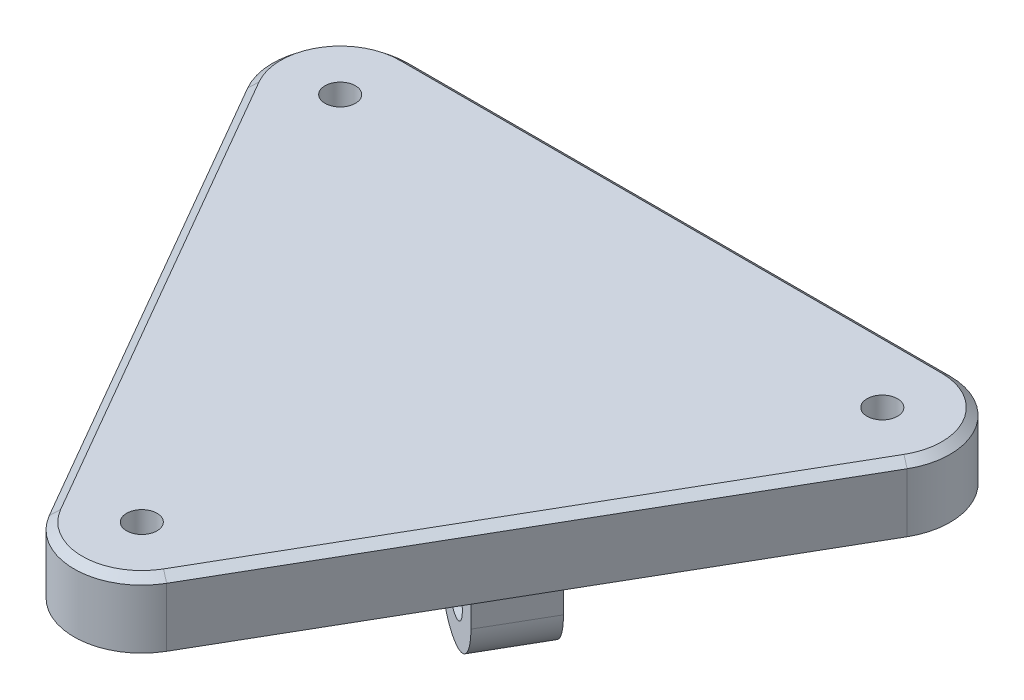
SolidWorks part; units mm, degrees
ref_plane "Front Plane" through (0, 0, 0) normal (0, 0, 1) x (1, 0, 0)
ref_plane "Top Plane" through (0, 0, 0) normal (0, 1, 0) x (1, 0, 0)
ref_plane "Right Plane" through (0, 0, 0) normal (1, 0, 0) x (0, 0, -1)
sketch "Sketch1" plane through (0, 0, 0) normal (0, 1, 0) x (1, 0, 0)
  line L0 (0, 18.75) -> (0, -14.7407) construction
  line L1 (-6.25, 0) -> (6.25, 0) construction
  line L7 (0, 0) -> (-16.238, -9.375) construction
  line L8 (0, 0) -> (16.238, -9.375) construction
  circle A3 centre (0, 0) radius 6.25
  point P2 (5.4127, -3.125)
  point P5 (0, 6.25)
  point P6 (-6.25, 0)
  point P7 (0, -6.25)
  point P8 (6.25, 0)
  point P11 (-5.4127, -3.125)
  dimension "D2" = 12.5
  dimension "D1" = 12.5
  dimension "D3" = 12.5
  dimension "D4" = 12.5
  dimension "D5" = 120
  dimension "D6" = 120
ref_plane "Plane4" through (0, 0, 0) normal (0, 1, 0) x (1, 0, 0)
sketch "Sketch6" plane through (0, 0, 0) normal (0, 1, 0) x (1, 0, 0)
  line L0 (-40, 33.094) -> (40, 33.094)
  line L1 (-28.6603, -16.547) -> (0, 0) construction
  line L2 (0, 0) -> (28.6603, -16.547) construction
  line L3 (28.6603, -16.547) -> (48.6603, 18.094)
  line L4 (-28.6603, -16.547) -> (-48.6603, 18.094)
  line L5 (-28.6603, -16.547) -> (-8.6603, -51.188)
  line L6 (8.6603, -51.188) -> (28.6603, -16.547)
  line L7 (0, 0) -> (-40, 23.094) construction
  line L8 (-40, 23.094) -> (40, 23.094) construction
  line L9 (40, 23.094) -> (0, 0) construction
  line L10 (0, 0) -> (0, -46.188) construction
  line L11 (0, 0) -> (-34.5631, 0) construction
  arc A0 (48.6603, 18.094) -> (40, 33.094) centre (40, 23.094) ccw
  arc A1 (-8.6603, -51.188) -> (8.6603, -51.188) centre (0, -46.188) ccw
  arc A2 (-48.6603, 18.094) -> (-40, 33.094) centre (-40, 23.094) cw
  dimension "D1" = 10
  dimension "D3" = 80
  dimension "D2" = 40
  dimension "D4" = 46.188
extrude "Boss-Extrude3" add sketch "Sketch6" along normal blind 10
ref_plane "Plane5" through (0, 10, 0) normal (0, 1, 0) x (1, 0, 0)
ref_plane "Plane10" through (0, 0, 0) normal (0, -1, 0) x (-1, 0, 0)
sketch "Sketch13" plane through (0, 0, 0) normal (0, -1, 0) x (-1, 0, 0)
  line L2 (-40, 33.094) -> (40, 33.094) construction
  line L3 (-5.25, 26.094) -> (4.75, 26.094)
  line L22 (-5.25, 26.094) -> (-5.25, 14.094)
  line L23 (-5.25, 14.094) -> (4.75, 14.094)
  line L24 (4.75, 14.094) -> (4.75, 26.094)
  point P0 (-0.25, 33.094)
  point P1 (-0.25, 26.094)
  point P5 (0, 33.094)
  dimension "D1" = 7
  dimension "D2" = 0.25
  dimension "D4" = 10
  dimension "D6" = 12
extrude "Boss-Extrude5" add sketch "Sketch13" along normal blind 20
ref_plane "Plane12" through (5.25, 0, 0) normal (1, 0, 0) x (0, 0, -1)
sketch "Sketch15" plane through (5.25, 0, 0) normal (1, 0, 0) x (0, 0, -1)
  line L0 (20.094, 0) -> (20.094, -8) construction
  line L1 (26.094, 0) -> (14.094, 0) construction
  line L2 (14.094, -8) -> (14.094, -20)
  line L3 (14.094, -20) -> (26.094, -20)
  line L4 (26.094, -20) -> (26.094, -8)
  circle A0 centre (20.094, -8) radius 2.55
  arc A1 (14.094, -8) -> (26.094, -8) centre (20.094, -8) ccw
  dimension "D2" = 5.1
  dimension "D1" = 8
extrude "Cut-Extrude7" cut sketch "Sketch15" against normal through all
ref_plane "Plane14" through (0, 10, 0) normal (0, 1, 0) x (1, 0, 0)
sketch "Sketch17" plane through (0, 10, 0) normal (0, 1, 0) x (1, 0, 0)
  line L0 (-40, 33.094) -> (40, 33.094) construction
  line L1 (0, 33.094) -> (0, 23.094) construction
ref_plane "Plane15" through (0, 0, 0) normal (0, -1, 0) x (-1, 0, 0)
ref_plane "Plane16" through (0, 0, 0) normal (0, -1, 0) x (-1, 0, 0)
sketch "Sketch18" plane through (0, 0, 0) normal (0, -1, 0) x (-1, 0, 0)
  point P10 (-40, 23.094)
  point P11 (40, 23.094)
  point P12 (0, -46.188)
ref_plane "Plane17" through (0, 0, 0) normal (0, -1, 0) x (-1, 0, 0)
hole_wizard "CBORE for M4 SHCS1" positions "Sketch19" profile "Sketch20" counterbore size "M4" standard "ANSI Metric"
sketch "Sketch19" plane through (0, 0, 0) normal (0, -1, 0) x (-1, 0, 0)
  point P0 (-40, 23.094)
  point P3 (40, 23.094)
  point P6 (0, -46.188)
sketch "Sketch20" plane through (40, 0, -23.094) normal (1, 0, 0) x (0, 0, -1)
  line L0 (0, 0) -> (0, 16.8519)
  line L1 (0, 16.8519) -> (2.25, 15.5)
  line L2 (2.25, 15.5) -> (2.25, 4)
  line L3 (2.25, 4) -> (4, 4)
  line L4 (4, 4) -> (4, 0)
  line L5 (4, 0) -> (0, 0)
  line L10 (0, 16.8519) -> (-2.25, 15.5) construction
  line L11 (0, -6.35) -> (0, 107.95) construction
  dimension "Hole Dia." = 4.5
  dimension "Hole Depth" = 15.5
  dimension "C'Bore Dia." = 8
  dimension "C'Bore Depth" = 4
  dimension "Drill Angle" = 118
sketch "Sketch21" plane through (0, 0, 0) normal (0, -1, 0) x (-1, 0, 0)
  circle A0 centre (0, 0) radius 1.118
extrude "Boss-Extrude6" add sketch "Sketch21" along normal blind 1
pattern_circular "CirPattern3" count 3 over 360 about axis through (0, 0, 0) along (0, 1, 0) of "Boss-Extrude6", "Cut-Extrude7", "Boss-Extrude5"
sketch "Sketch22" plane through (0, -1, 0) normal (0, -1, 0) x (-1, 0, 0)
  circle A0 centre (0, 0) radius 1.118
  circle A1 centre (0, 0) radius 1.118 construction
extrude "Cut-Extrude8" cut sketch "Sketch22" against normal up to surface (1 mm away) up to face at (17.2769, 0, 10.2635)
fillet "Fillet1" radius 4 12 edges at (-20.0269, 0, 5.5004) (-15.0269, 0, 14.1606) (-12.3308, 0, 6.8305) (5.25, 0, -20.094) (0.25, 0, -14.094) (-4.75, 0, -20.094) (12.0808, 0, 7.2635) (19.7769, 0, 5.9334) (14.7769, 0, 14.5936) (0.25, 0, -26.094) (22.4731, 0, 13.2635) (-22.7231, 0, 12.8305)
chamfer "Chamfer1" distance 1 angle 50.84 6 edges at (48.6603, 10, -28.094) (0, 10, -33.094) (28.6603, 10, 16.547) (-48.6603, 10, -28.094) (0, 10, 56.188) (-28.6603, 10, 16.547)
chamfer "Chamfer2" distance 1 angle 17.09 6 edges at (-48.6603, 0, -28.094) (-28.6603, 0, 16.547) (0, 0, -33.094) (0, 0, 56.188) (48.6603, 0, -28.094) (28.6603, 0, 16.547)
